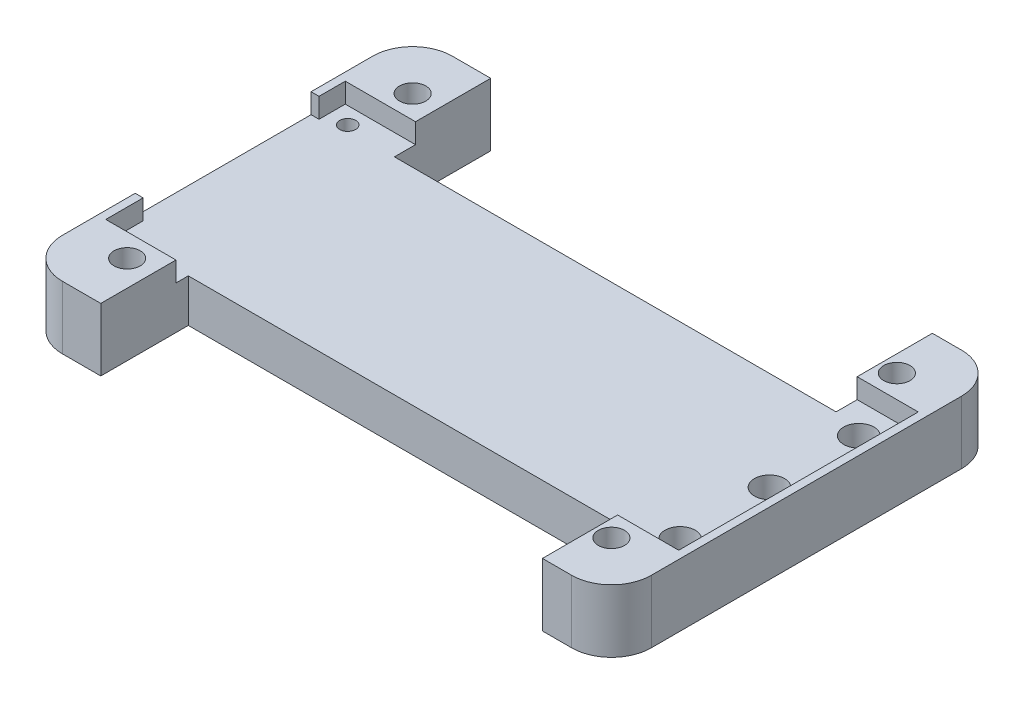
SolidWorks part; units mm, degrees
ref_plane "Front Plane" through (0, 0, 0) normal (0, 0, 1) x (1, 0, 0)
ref_plane "Top Plane" through (0, 0, 0) normal (0, 1, 0) x (1, 0, 0)
ref_plane "Right Plane" through (0, 0, 0) normal (1, 0, 0) x (0, 0, -1)
sketch "Sketch1" plane through (0, 0, 0) normal (0, 1, 0) x (1, 0, 0)
  line L1 (-37, -24.5) -> (37, -24.5)
  line L2 (-37, -24.5) -> (-37, 24.5)
  line L3 (-37, 24.5) -> (37, 24.5)
  line L4 (37, -24.5) -> (37, 24.5)
  line L5 (-37, -24.5) -> (37, 24.5) construction
  line L6 (-37, 24.5) -> (37, -24.5) construction
  point P0 (0, 0)
  dimension "D1" = 74
  dimension "D2" = 49
extrude "Boss-Extrude1" add sketch "Sketch1" along normal blind 7.9
sketch "Sketch3" plane through (0, 7.9, 0) normal (0, 1, 0) x (1, 0, 0)
  line L1 (-30.424, -17.9375) -> (30.424, -17.9375) construction
  line L2 (-30.424, -17.9375) -> (-30.424, 17.9375) construction
  line L3 (-30.424, 17.9375) -> (30.424, 17.9375) construction
  line L4 (30.424, -17.9375) -> (30.424, 17.9375) construction
  line L5 (-30.424, -17.9375) -> (30.424, 17.9375) construction
  line L6 (-30.424, 17.9375) -> (30.424, -17.9375) construction
  circle A0 centre (-30.424, 17.9375) radius 1.65
  circle A1 centre (30.424, 17.9375) radius 1.65
  circle A2 centre (-30.424, -17.9375) radius 1.65
  circle A3 centre (30.424, -17.9375) radius 1.65
  point P0 (0, 0)
  dimension "D3" = 3.3
  dimension "D4" = 3.3
  dimension "D5" = 3.3
  dimension "D6" = 3.3
  dimension "D1" = 60.848
  dimension "D2" = 35.875
fillet "Fillet1" radius 5 4 edges at (-37, 3.95, 24.5) (-37, 3.95, -24.5) (37, 3.95, 24.5) (37, 3.95, -24.5)
extrude "Cut-Extrude6" cut sketch "Sketch3" against normal blind 7.9
sketch "Sketch9" plane through (0, 7.9, 0) normal (0, 1, 0) x (1, 0, 0)
  line L0 (30.424, 17.9375) -> (30.424, -17.9375) construction
  line L1 (30.424, 17.9375) -> (45.424, 17.9375) construction
  line L2 (30.424, -17.9375) -> (45.424, -17.9375) construction
  line L3 (-30.424, 17.9375) -> (-45.424, 17.9375) construction
  line L4 (-30.424, 17.9375) -> (-30.424, -17.9375) construction
  circle A0 centre (32.354, 11.2275) radius 1.9
  circle A3 centre (32.354, 0.0025) radius 1.9
  circle A4 centre (32.354, -11.2275) radius 1.9
  circle A6 centre (-33.584, 12.9375) radius 1
  point P10 (30.424, 0)
  dimension "D1" = 3.8
  dimension "D2" = 3.8
  dimension "D3" = 3.8
  dimension "D11" = 2
  dimension "D4" = 1.93
  dimension "D5" = 1.93
  dimension "D6" = 1.93
  dimension "D7" = 6.71
  dimension "D8" = 6.71
  dimension "D9" = 11.23
  dimension "D10" = 11.225
  dimension "D12" = 3.16
  dimension "D13" = 5
extrude "Cut-Extrude7" cut sketch "Sketch9" against normal blind 7.9
sketch "Sketch10" plane through (0, 7.9, 0) normal (0, 1, 0) x (1, 0, 0)
  line L0 (-37, 19.5) -> (-37, -19.5) construction
  line L1 (-37, 15.05) -> (37, 15.05) construction
  line L3 (-37, -15.05) -> (37, -15.05) construction
  line L4 (37, 15.05) -> (37, -15.05) construction
  line L5 (37, -19.5) -> (37, 19.5) construction
  line L6 (-32, -24.5) -> (32, -24.5) construction
  line L7 (32, 24.5) -> (-32, 24.5) construction
  line L8 (-37, 15.05) -> (36, 15.05) construction
  line L9 (36, 15.05) -> (36, -15.05)
  line L10 (36, -15.05) -> (-37, -15.05) construction
  line L16 (-36, 15.05) -> (-36, 11.75)
  line L17 (-36, 11.75) -> (-37, 11.75)
  line L18 (-37, 11.75) -> (-37, -10.35)
  line L19 (-37, -10.35) -> (-36, -10.35)
  line L20 (-36, -10.35) -> (-36, -15.05)
  line L21 (-36, 15.05) -> (36, 15.05)
  line L22 (-36, -15.05) -> (36, -15.05)
  dimension "D1" = 9.45
  dimension "D2" = 9.45
  dimension "D3" = 30.1
  dimension "D4" = 1
  dimension "D5" = 1
  dimension "D6" = 1
  dimension "D7" = 3.3
  dimension "D8" = 4.7
  dimension "D9" = 22.1
extrude "Cut-Extrude8" cut sketch "Sketch10" against normal blind 2.5
sketch "Sketch11" plane through (0, 7.9, 0) normal (0, 1, 0) x (1, 0, 0)
  line L0 (32, 24.5) -> (-32, 24.5) construction
  line L1 (-27.176, 24.5) -> (28.324, 24.5)
  line L2 (-27.176, 24.5) -> (-27.176, 12.4)
  line L3 (-27.176, 12.4) -> (28.324, 12.4)
  line L4 (28.324, 24.5) -> (28.324, 12.4)
  circle A0 centre (30.424, 17.9375) radius 1.65 construction
  circle A1 centre (-30.424, 17.9375) radius 1.65 construction
  dimension "D3" = 2.1
  dimension "D1" = 12.1
  dimension "D2" = 55.5
  dimension "D4" = 3.248
extrude "Cut-Extrude9" cut sketch "Sketch11" against normal blind 7.9
sketch "Sketch12" plane through (0, 7.9, 0) normal (0, 1, 0) x (1, 0, 0)
  line L2 (-27.176, -15.05) -> (-27.176, -24.5) construction
  line L3 (-27.176, -24.5) -> (28.324, -24.5) construction
  line L4 (28.324, -15.05) -> (28.324, -24.5) construction
  line L5 (-32, -24.5) -> (32, -24.5) construction
  line L6 (-27.176, -15.05) -> (-27.176, -13.5)
  line L7 (-27.176, -13.5) -> (28.324, -13.5)
  line L8 (28.324, -13.5) -> (28.324, -15.05)
  line L9 (-27.176, -15.05) -> (-27.176, -21.5)
  line L10 (-27.176, -21.5) -> (28.324, -21.5)
  line L11 (28.324, -21.5) -> (28.324, -15.05)
  circle A0 centre (30.424, -17.9375) radius 1.65 construction
  dimension "D1" = 2.1
  dimension "D2" = 55.5
  dimension "D3" = 11
  dimension "D4" = 8
extrude "Cut-Extrude10" cut sketch "Sketch12" against normal blind 7.9
sketch "Sketch14" plane through (0, 5.4, 0) normal (0, 1, 0) x (1, 0, 0)
  line L0 (-27.176, 12.4) -> (28.324, 12.4) construction
  line L1 (-8, 10.4) -> (15, 10.4)
  line L2 (-8, 10.4) -> (-8, -11.6)
  line L3 (-8, -11.6) -> (15, -11.6)
  line L4 (15, 10.4) -> (15, -11.6)
  line L6 (-37, -10.35) -> (-37, -19.5) construction
  dimension "D1" = 23
  dimension "D2" = 22
  dimension "D3" = 2
  dimension "D4" = 29
sketch "Sketch15" plane through (0, 7.9, 0) normal (0, 1, 0) x (1, 0, 0)
  line L0 (-27.176, -21.5) -> (-27.176, -24.5)
  line L1 (-32, -24.5) -> (32, -24.5) construction
  line L2 (28.324, -21.5) -> (28.324, -24.5)
  line L3 (-27.176, -21.5) -> (28.324, -21.5)
  line L4 (-27.176, -24.5) -> (28.324, -24.5)
extrude "Cut-Extrude11" cut sketch "Sketch15" against normal blind 10
